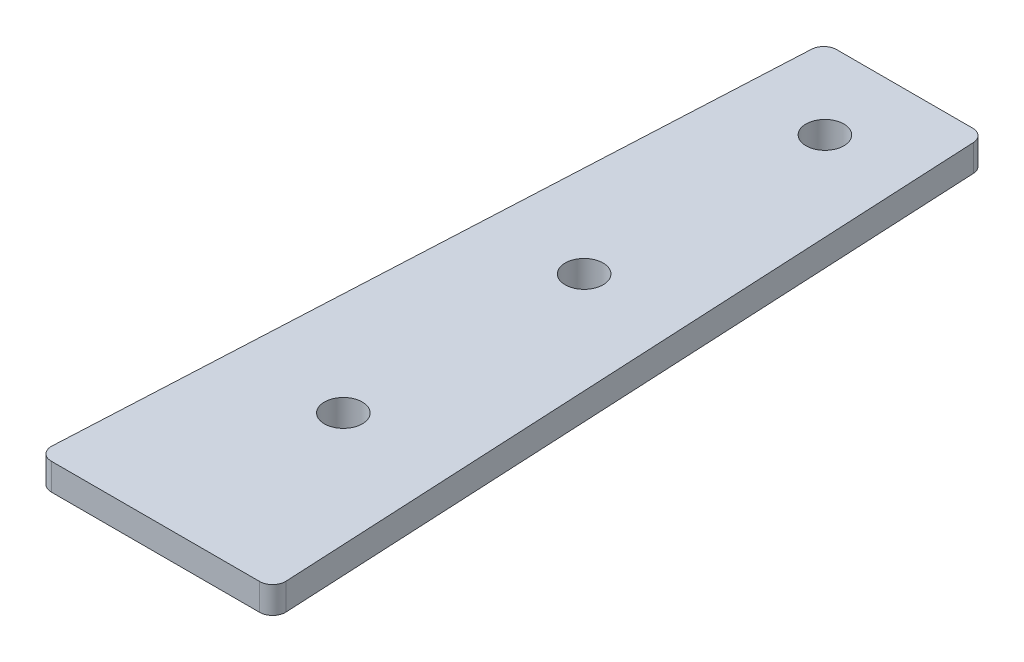
SolidWorks part; units mm, degrees
material "ASTM A36 Steel"
ref_plane "X-Y Datum" through (0, 0, 0) normal (0, 0, 1) x (1, 0, 0)
ref_plane "X-Z Datum" through (0, 0, 0) normal (0, 1, 0) x (1, 0, 0)
ref_plane "Y-Z Datum" through (0, 0, 0) normal (1, 0, 0) x (0, 0, -1)
sketch "Sketch1" plane through (0, 0, 0) normal (0, 1, 0) x (1, 0, 0)
  line L0 (-91.83, 0) -> (49908.17, 0) construction
  line L1 (-91.83, 38.035) -> (91.83, 38.035) construction
  line L2 (-91.83, 38.035) -> (-91.83, -38.035) construction
  line L3 (-91.83, -38.035) -> (91.83, -38.035) construction
  line L4 (91.83, 38.035) -> (91.83, -38.035) construction
  line L5 (-91.83, 38.035) -> (91.83, -38.035) construction
  line L6 (-91.83, -38.035) -> (91.83, 38.035) construction
  line L7 (-115.0883, 28.575) -> (49884.9117, 28.575) construction
  line L8 (-116.2913, -28.575) -> (49883.7087, -28.575) construction
  line L9 (-75.32, 54.5103) -> (-75.32, -49945.4897) construction
  line L10 (75.32, 62.9314) -> (75.32, -49937.0686) construction
  line L11 (-75.32, 38.035) -> (-67.2447, 38.035)
  line L12 (-75.32, 38.035) -> (-83.3953, 38.035)
  line L14 (-75.32, -50.865) -> (-62.9521, -50.865)
  line L15 (-75.32, -50.865) -> (-87.6879, -50.865)
  line L16 (-84.9174, 36.5871) -> (-89.21, -49.2649)
  line L17 (-65.7226, 36.5871) -> (-61.43, -49.2649)
  arc A0 (-62.9521, -50.865) -> (-61.43, -49.2649) centre (-62.9521, -49.341) ccw
  arc A1 (-87.6879, -50.865) -> (-89.21, -49.2649) centre (-87.6879, -49.341) cw
  arc A2 (-67.2447, 38.035) -> (-65.7226, 36.5871) centre (-67.2447, 36.511) cw
  arc A3 (-83.3953, 38.035) -> (-84.9174, 36.5871) centre (-83.3953, 36.511) ccw
  point P0 (0, 0)
  point P8 (-91.83, 0)
  point P25 (-61.35, -50.865)
  point P28 (-89.29, -50.865)
  point P31 (-65.795, 38.035)
  point P34 (-84.845, 38.035)
  dimension "D12" = 1.524
  dimension "D1" = 183.66
  dimension "D2" = 76.07
  dimension "D3" = 28.575
  dimension "D4" = 28.575
  dimension "D5" = 16.51
  dimension "D6" = 16.51
  dimension "D7" = 9.525
  dimension "D8" = 9.525
  dimension "D9" = 88.9
  dimension "D10" = 13.97
  dimension "D11" = 13.97
extrude "Boss-Extrude1" add sketch "Sketch1" along normal blind 3.175
sketch "Sketch4" plane through (0, 0, 0) normal (0, 1, 0) x (1, 0, 0)
  line L0 (-91.83, 0) -> (49908.17, 0) construction
  line L1 (-91.83, 38.035) -> (91.83, 38.035) construction
  line L2 (-91.83, 38.035) -> (-91.83, -38.035) construction
  line L3 (-91.83, -38.035) -> (91.83, -38.035) construction
  line L4 (91.83, 38.035) -> (91.83, -38.035) construction
  line L5 (-91.83, 38.035) -> (91.83, -38.035) construction
  line L6 (-91.83, -38.035) -> (91.83, 38.035) construction
  line L7 (-115.0883, 28.575) -> (49884.9117, 28.575) construction
  line L8 (-116.2913, -28.575) -> (49883.7087, -28.575) construction
  line L9 (-75.32, 54.5103) -> (-75.32, -49945.4897) construction
  line L10 (75.32, 62.9314) -> (75.32, -49937.0686) construction
  line L11 (-75.32, 38.035) -> (-67.2447, 38.035)
  line L12 (-75.32, 38.035) -> (-83.3953, 38.035)
  line L14 (-75.32, -50.865) -> (-62.9521, -50.865)
  line L15 (-75.32, -50.865) -> (-87.6879, -50.865)
  line L16 (-84.9174, 36.5871) -> (-89.21, -49.2649)
  line L17 (-65.7226, 36.5871) -> (-61.43, -49.2649)
  arc A0 (-62.9521, -50.865) -> (-61.43, -49.2649) centre (-62.9521, -49.341) ccw
  arc A1 (-87.6879, -50.865) -> (-89.21, -49.2649) centre (-87.6879, -49.341) cw
  arc A2 (-67.2447, 38.035) -> (-65.7226, 36.5871) centre (-67.2447, 36.511) cw
  arc A3 (-83.3953, 38.035) -> (-84.9174, 36.5871) centre (-83.3953, 36.511) ccw
  point P0 (0, 0)
  point P8 (-91.83, 0)
  point P25 (-61.35, -50.865)
  point P28 (-89.29, -50.865)
  point P31 (-65.795, 38.035)
  point P34 (-84.845, 38.035)
  dimension "D12" = 1.524
  dimension "D1" = 183.66
  dimension "D2" = 76.07
  dimension "D3" = 28.575
  dimension "D4" = 28.575
  dimension "D5" = 16.51
  dimension "D6" = 16.51
  dimension "D7" = 9.525
  dimension "D8" = 9.525
  dimension "D9" = 88.9
  dimension "D10" = 13.97
  dimension "D11" = 13.97
hole_wizard "M4 Clearance Hole1" positions "Sketch5" profile "Sketch6" hole size "M4" standard "ANSI Metric" end condition through all
sketch "Sketch5" plane through (0, 3.175, 0) normal (0, 1, 0) x (1, 0, 0)
  line L0 (-200115.0883, 28.575) -> (249884.9117, 28.575) construction
  line L1 (-75.32, 200054.5103) -> (-75.32, -249945.4897) construction
  line L2 (-200091.83, 0) -> (249908.17, 0) construction
  line L3 (-200116.2913, -28.575) -> (249883.7087, -28.575) construction
  point P0 (-75.32, 28.575)
  point P6 (-75.32, 0)
  point P10 (-75.32, -28.575)
sketch "Sketch6" plane through (-75.32, 3.175, -28.575) normal (1, 0, 0) x (0, 0, 1)
  line L0 (0, 0) -> (0, 3.175)
  line L1 (0, 3.175) -> (2.25, 3.175)
  line L2 (2.25, 3.175) -> (2.25, 0)
  line L5 (2.25, 0) -> (0, 0)
  line L11 (0, -6.35) -> (0, 107.95) construction
  dimension "Thru Hole Dia." = 4.5
  dimension "Thru Hole Depth" = 3.175
